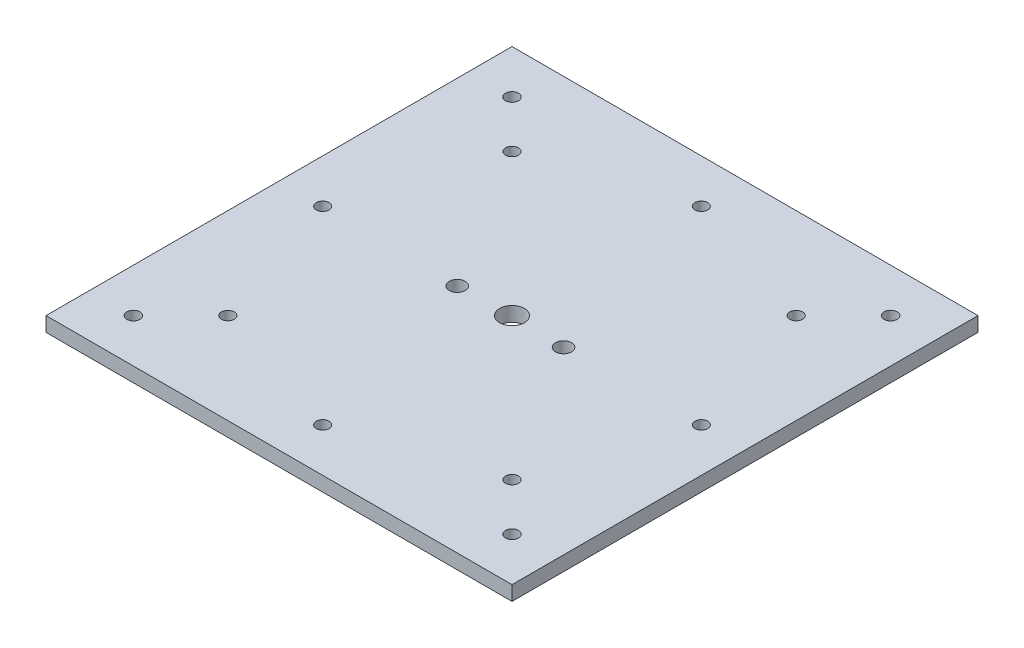
SolidWorks part; units mm, degrees
ref_plane "Front Plane" through (0, 0, 0) normal (0, 0, 1) x (1, 0, 0)
ref_plane "Top Plane" through (0, 0, 0) normal (0, 1, 0) x (1, 0, 0)
ref_plane "Right Plane" through (0, 0, 0) normal (1, 0, 0) x (0, 0, -1)
sketch "Sketch1" plane through (0, 0, 0) normal (0, 1, 0) x (1, 0, 0)
  line L0 (0, 80) -> (0, -80) construction
  line L1 (-80, 80) -> (80, 80)
  line L2 (-80, 80) -> (-80, -80)
  line L3 (-80, -80) -> (80, -80)
  line L4 (80, 80) -> (80, -80)
  line L5 (-80, 80) -> (80, -80) construction
  line L6 (-80, -80) -> (80, 80) construction
  circle A0 centre (0, 0) radius 69 construction
  circle A2 centre (48.7904, 48.7904) radius 2.2
  circle A4 centre (48.7904, -48.7904) radius 2.2
  circle A6 centre (-48.7904, -48.7904) radius 2.2
  circle A8 centre (-48.7904, 48.7904) radius 2.2
  circle A9 centre (0, 0) radius 4.25
  circle A10 centre (18.2724, -0.5716) radius 2.75
  circle A11 centre (-18.2276, -0.5716) radius 2.75
  circle A12 centre (0, 0) radius 65 construction
  circle A13 centre (0, 65) radius 2.2
  circle A14 centre (65, 0) radius 2.2
  circle A15 centre (0, -65) radius 2.2
  circle A16 centre (-65, 0) radius 2.2
  circle A18 centre (-65, 65) radius 2.25
  circle A19 centre (65, 65) radius 2.25
  circle A20 centre (65, -65) radius 2.25
  circle A21 centre (-65, -65) radius 2.25
  point P0 (0, 0)
  point P13 (0, 0)
  point P16 (0, 0)
  point P19 (0, 0)
  point P22 (0, 0)
  point P25 (0, 0)
  point P28 (0, 0)
  point P31 (0, 0)
  point P34 (0, 0)
  point P43 (0, 0)
  dimension "D3" = 8
  dimension "D4" = 4
  dimension "D5" = 160
  dimension "D6" = 15
  dimension "D1" = 160
  dimension "D2" = 160
  dimension "D7" = 15
  dimension "D10" = 15
  dimension "D11" = 15
  dimension "D12" = 15
  dimension "D13" = 15
  dimension "D8" = 2
  dimension "D9" = 2
extrude "Boss-Extrude1" add sketch "Sketch1" along normal blind 5
